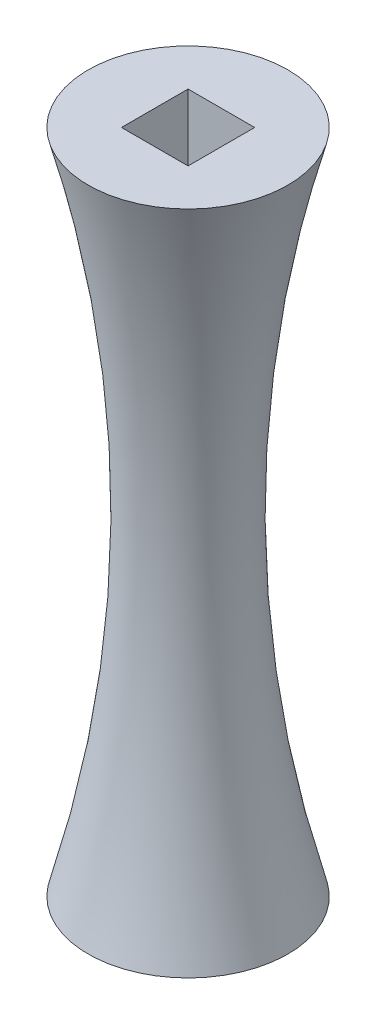
SolidWorks part; units mm, degrees
ref_plane "前视基准面" through (0, 0, 0) normal (0, 0, 1) x (1, 0, 0)
ref_plane "上视基准面" through (0, 0, 0) normal (0, 1, 0) x (1, 0, 0)
ref_plane "右视基准面" through (0, 0, 0) normal (1, 0, 0) x (0, 0, -1)
other "Configuration Table"
sketch "草图1" plane through (0, 0, 0) normal (0, 1, 0) x (1, 0, 0)
  line L5 (0, 7.5) -> (0, -7.5) construction
  line L6 (-7.5, 0) -> (7.5, 0) construction
  circle A0 centre (0, 0) radius 7.5
  point P0 (0, 0)
extrude "凸台-拉伸1" add sketch "草图1" along normal blind 50
sketch "草图2" plane through (0, 50, 0) normal (0, 1, 0) x (1, 0, 0)
  line L0 (-7.5, 7.5) -> (7.5, -7.5) construction
  line L2 (-2.5, 2.5) -> (2.5, 2.5)
  line L3 (-2.5, 2.5) -> (-2.5, -2.5)
  line L4 (-2.5, -2.5) -> (2.5, -2.5)
  line L5 (2.5, 2.5) -> (2.5, -2.5)
  line L6 (0, -2.5) -> (0, 2.5) construction
  line L7 (-2.5, 0) -> (2.5, 0) construction
  point P4 (0, 0)
  dimension "D1" = 5
extrude "切除-拉伸1" cut sketch "草图2" against normal blind 10
sketch "草图3" plane through (0, 0, 0) normal (0, -1, 0) x (1, 0, 0)
  line L1 (-2.5, 2.5) -> (2.5, 2.5)
  line L2 (-2.5, 2.5) -> (-2.5, -2.5)
  line L3 (-2.5, -2.5) -> (2.5, -2.5)
  line L4 (2.5, 2.5) -> (2.5, -2.5)
extrude "切除-拉伸2" cut sketch "草图3" against normal blind 10
sketch "草图4" plane through (0, 0, 0) normal (1, 0, 0) x (0, 0, -1)
  line L0 (-7.5, 50) -> (-7.5, 0) construction
  line L1 (7.5, 50) -> (-7.5, 50) construction
  line L2 (-7.5, 0) -> (7.5, 0) construction
  line L3 (-7.5, 50) -> (-7.5, 0)
  line L4 (0, 0) -> (0, 50) construction
  line L5 (-2.5, 50) -> (2.5, 50) construction
  arc A0 (-7.5, 50) -> (-7.5, 0) centre (-97.5, 25) cw
  dimension "D1" = 0
  dimension "D2" = 0
  dimension "D3" = 90
revolve "切除-旋转1" cut sketch "草图4" angle 360 about L4
